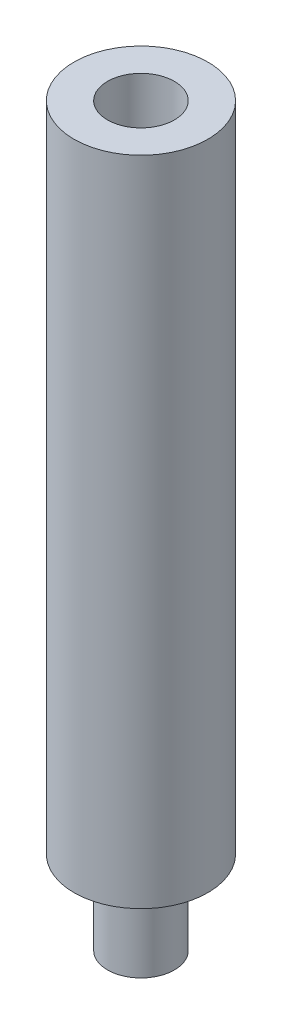
SolidWorks part; units mm, degrees
ref_plane "Plan de face" through (0, 0, 0) normal (0, 0, 1) x (1, 0, 0)
ref_plane "Plan de dessus" through (0, 0, 0) normal (0, 1, 0) x (1, 0, 0)
ref_plane "Plan de droite" through (0, 0, 0) normal (1, 0, 0) x (0, 0, -1)
sketch "Esquisse1" plane through (0, 0, 0) normal (0, 1, 0) x (1, 0, 0)
  circle A1 centre (0, 0) radius 4
  dimension "D2" = 8
extrude "Boss.-Extru.1" add sketch "Esquisse1" against normal blind 39
sketch "Esquisse3" plane through (0, 0, 0) normal (0, 1, 0) x (1, 0, 0)
  circle A0 centre (0, 0) radius 2
  dimension "D1" = 4
extrude "Enlèv. mat.-Extru.1" cut sketch "Esquisse3" against normal blind 10
sketch "Esquisse4" plane through (0, -39, 0) normal (0, -1, 0) x (1, 0, 0)
  circle A0 centre (0, 0) radius 2
  dimension "D1" = 4
extrude "Boss.-Extru.2" add sketch "Esquisse4" along normal blind 5
